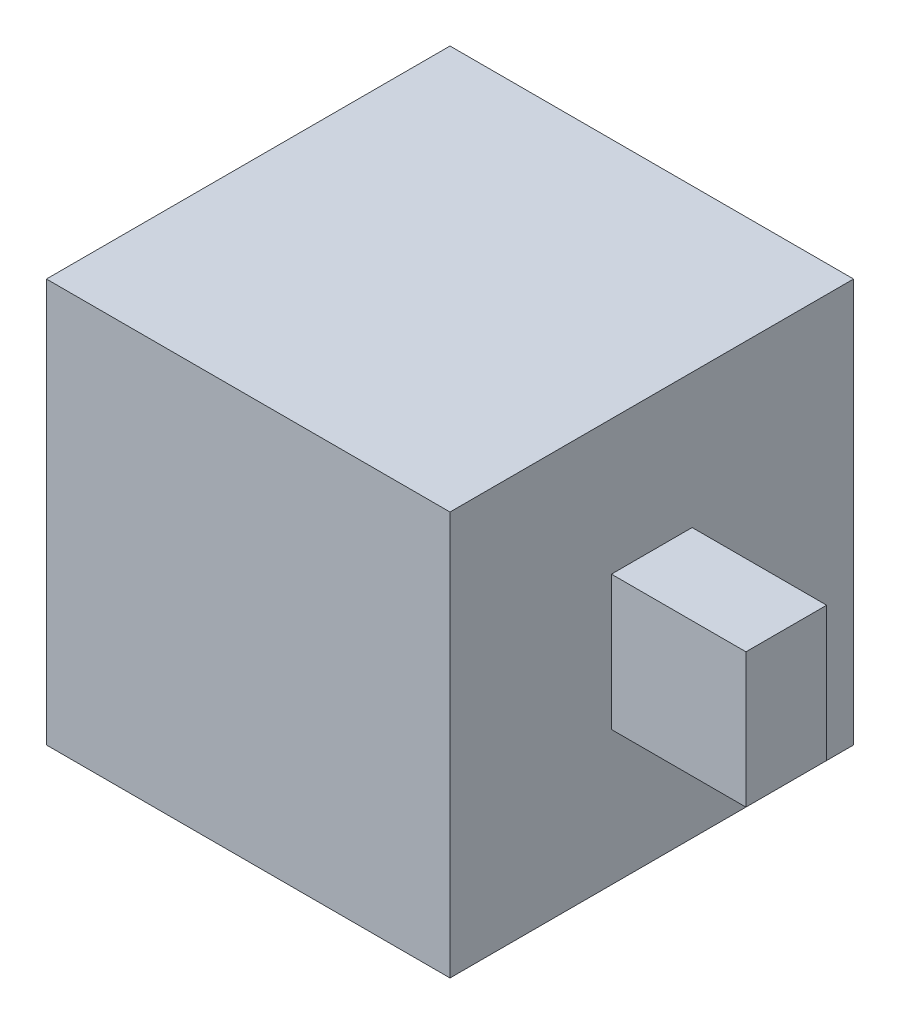
SolidWorks part; units mm, degrees
ref_plane "前视基准面" through (0, 0, 0) normal (0, 0, 1) x (1, 0, 0)
ref_plane "上视基准面" through (0, 0, 0) normal (0, 1, 0) x (1, 0, 0)
ref_plane "右视基准面" through (0, 0, 0) normal (1, 0, 0) x (0, 0, -1)
other "Configuration Table"
sketch "草图1" plane through (0, 0, 0) normal (1, 0, 0) x (0, 0, -1)
  line L1 (0, 0) -> (30, 0)
  line L2 (0, 0) -> (0, 30)
  line L3 (0, 30) -> (30, 30)
  line L4 (30, 0) -> (30, 30)
  dimension "D1" = 30
  dimension "D2" = 30
extrude "凸台-拉伸1" add sketch "草图1" along normal blind 30
sketch "草图2" plane through (30, 0, 0) normal (1, 0, 0) x (0, 0, -1)
  line L2 (30, 0) -> (30, 30) construction
  line L3 (12, 20) -> (18, 20)
  line L4 (12, 20) -> (12, 10)
  line L5 (12, 10) -> (18, 10)
  line L6 (18, 20) -> (18, 10)
  line L7 (0, 0) -> (30, 0) construction
  dimension "D1" = 6
  dimension "D2" = 10
  dimension "D3" = 12
  dimension "D4" = 10
extrude "凸台-拉伸2" add sketch "草图2" along normal blind 10 contours L3 L6 L5 L4
